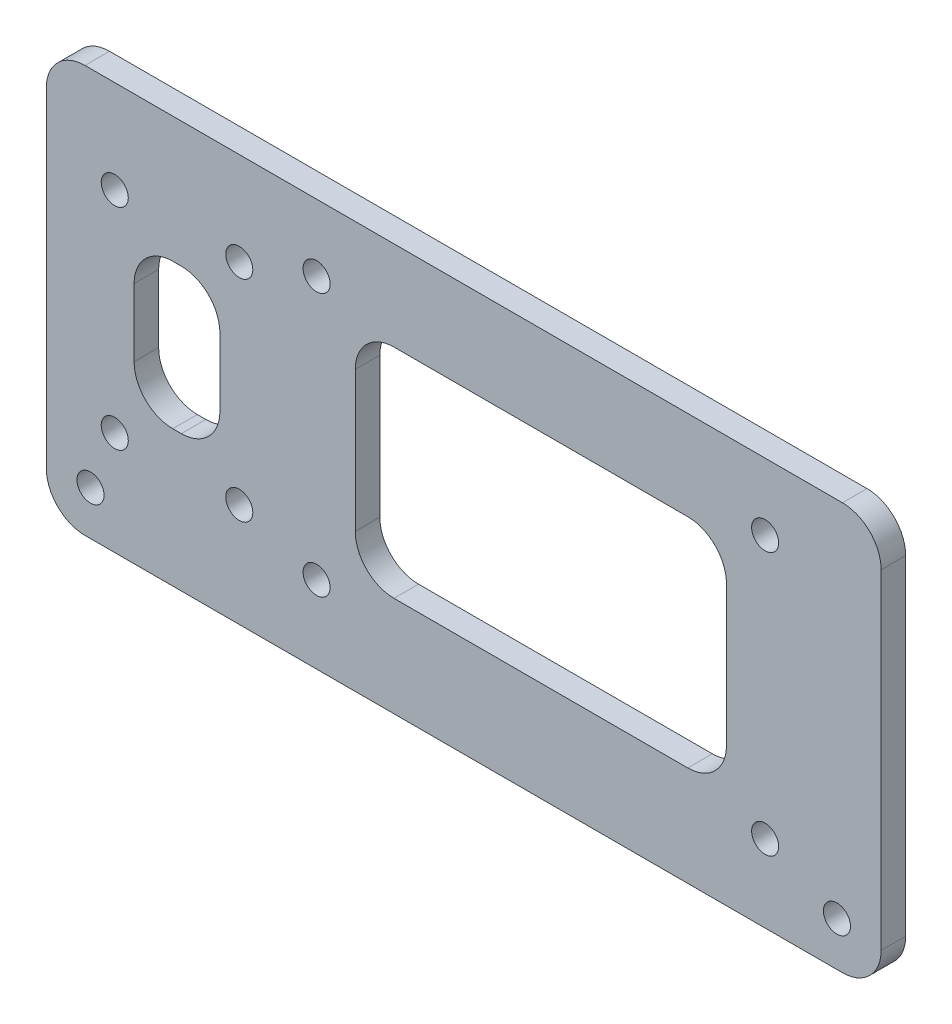
SolidWorks part; units mm, degrees
ref_plane "Front" through (0, 0, 0) normal (0, 0, 1) x (1, 0, 0)
ref_plane "Top" through (0, 0, 0) normal (0, 1, 0) x (1, 0, 0)
ref_plane "Right" through (0, 0, 0) normal (1, 0, 0) x (0, 0, -1)
sketch "Sketch1" plane through (0, 0, 0) normal (0, 0, 1) x (1, 0, 0)
  line L1 (-53.975, -43.815) -> (53.975, -43.815)
  line L2 (-53.975, -43.815) -> (-53.975, 43.815)
  line L3 (-53.975, 43.815) -> (53.975, 43.815)
  line L4 (53.975, -43.815) -> (53.975, 43.815)
  line L5 (-53.975, -43.815) -> (53.975, 43.815) construction
  line L6 (-53.975, 43.815) -> (53.975, -43.815) construction
  point P0 (0, 0)
  dimension "D1" = 107.95
  dimension "D2" = 87.63
extrude "Boss-Extrude1" add sketch "Sketch1" along normal blind 3.175
sketch "Sketch2" plane through (0, 0, 3.175) normal (0, 0, 1) x (1, 0, 0)
  line L1 (-48.26, -38.1) -> (48.26, -38.1) construction
  line L2 (-48.26, -38.1) -> (-48.26, 38.1) construction
  line L3 (-48.26, 38.1) -> (48.26, 38.1) construction
  line L4 (48.26, -38.1) -> (48.26, 38.1) construction
  line L5 (-48.26, -38.1) -> (48.26, 38.1) construction
  line L6 (-48.26, 38.1) -> (48.26, -38.1) construction
  circle A0 centre (-48.26, 38.1) radius 1.75
  circle A1 centre (48.26, 38.1) radius 1.75
  circle A2 centre (48.26, -38.1) radius 1.75
  circle A3 centre (-48.26, -38.1) radius 1.75
  point P0 (0, 0)
  dimension "D1" = 3.5
  dimension "D2" = 96.52
  dimension "D3" = 76.2
extrude "Cut-Extrude1" cut sketch "Sketch2" against normal through all
sketch "Sketch3" plane through (0, 0, 3.175) normal (0, 0, 1) x (1, 0, 0)
  line L0 (-53.975, -43.815) -> (53.975, -43.815) construction
  line L1 (-19.025, -33.815) -> (38.975, -33.815) construction
  line L2 (-19.025, -33.815) -> (-19.025, 0.185) construction
  line L3 (-19.025, 0.185) -> (38.975, 0.185) construction
  line L4 (38.975, -33.815) -> (38.975, 0.185) construction
  line L5 (-19.025, -33.815) -> (38.975, 0.185) construction
  line L6 (-19.025, 0.185) -> (38.975, -33.815) construction
  line L7 (53.975, -43.815) -> (53.975, 43.815) construction
  line L9 (-45.125, -30.415) -> (-29.025, -30.415) construction
  line L10 (-45.125, -30.415) -> (-45.125, -3.215) construction
  line L11 (-45.125, -3.215) -> (-29.025, -3.215) construction
  line L12 (-29.025, -30.415) -> (-29.025, -3.215) construction
  line L13 (-45.125, -30.415) -> (-29.025, -3.215) construction
  line L14 (-45.125, -3.215) -> (-29.025, -30.415) construction
  line L15 (-14.025, -2.746) -> (33.975, -2.746)
  line L16 (-14.025, -2.746) -> (-14.025, -30.884)
  line L17 (-14.025, -30.884) -> (33.975, -30.884)
  line L18 (33.975, -2.746) -> (33.975, -30.884)
  line L19 (-14.025, -2.746) -> (33.975, -30.884) construction
  line L20 (-14.025, -30.884) -> (33.975, -2.746) construction
  line L21 (-42.625, -7.4386) -> (-31.525, -7.4386)
  line L22 (-42.625, -7.4386) -> (-42.625, -26.1914)
  line L23 (-42.625, -26.1914) -> (-31.525, -26.1914)
  line L24 (-31.525, -7.4386) -> (-31.525, -26.1914)
  line L25 (-42.625, -7.4386) -> (-31.525, -26.1914) construction
  line L26 (-42.625, -26.1914) -> (-31.525, -7.4386) construction
  circle A0 centre (-29.025, -3.215) radius 1.75
  circle A1 centre (-29.025, -30.415) radius 1.75
  circle A2 centre (-45.125, -30.415) radius 1.75
  circle A3 centre (-45.125, -3.215) radius 1.75
  circle A4 centre (-19.025, -33.815) radius 1.75
  circle A5 centre (38.975, -33.815) radius 1.75
  circle A6 centre (38.975, 0.185) radius 1.75
  circle A7 centre (-19.025, 0.185) radius 1.75
  circle A8 centre (-48.26, -38.1) radius 1.75 construction
  point P0 (9.975, -16.815)
  point P9 (-37.075, -16.815)
  point P24 (9.975, -16.815)
  point P29 (-37.075, -16.815)
  point P34 (-31.525, -16.815)
  dimension "D1" = 34
  dimension "D2" = 58
  dimension "D3" = 10
  dimension "D4" = 15
  dimension "D5" = 27.2
  dimension "D6" = 16.1
  dimension "D7" = 10
  dimension "D8" = 5
  dimension "D9" = 10
extrude "Cut-Extrude2" cut sketch "Sketch3" against normal through all
sketch "Sketch4" plane through (0, 0, 3.175) normal (0, 0, 1) x (1, 0, 0)
  line L0 (53.975, -43.815) -> (53.975, 43.815) construction
  line L1 (-53.975, 43.815) -> (53.975, 43.815)
  line L2 (-53.975, 43.815) -> (-53.975, 8.815)
  line L3 (-53.975, 8.815) -> (53.975, 8.815)
  line L4 (53.975, 43.815) -> (53.975, 8.815)
  dimension "D1" = 35
extrude "Cut-Extrude3" cut sketch "Sketch4" against normal through all
fillet "Fillet1" radius 5 12 edges at (-53.975, -43.815, 1.5875) (53.975, -43.815, 1.5875) (53.975, 8.815, 1.5875) (-53.975, 8.815, 1.5875) (-42.625, -7.4386, 1.5875) (-42.625, -26.1914, 1.5875) (-31.525, -26.1914, 1.5875) (-31.525, -7.4386, 1.5875) (33.975, -2.746, 1.5875) (-14.025, -2.746, 1.5875) (-14.025, -30.884, 1.5875) (33.975, -30.884, 1.5875)
